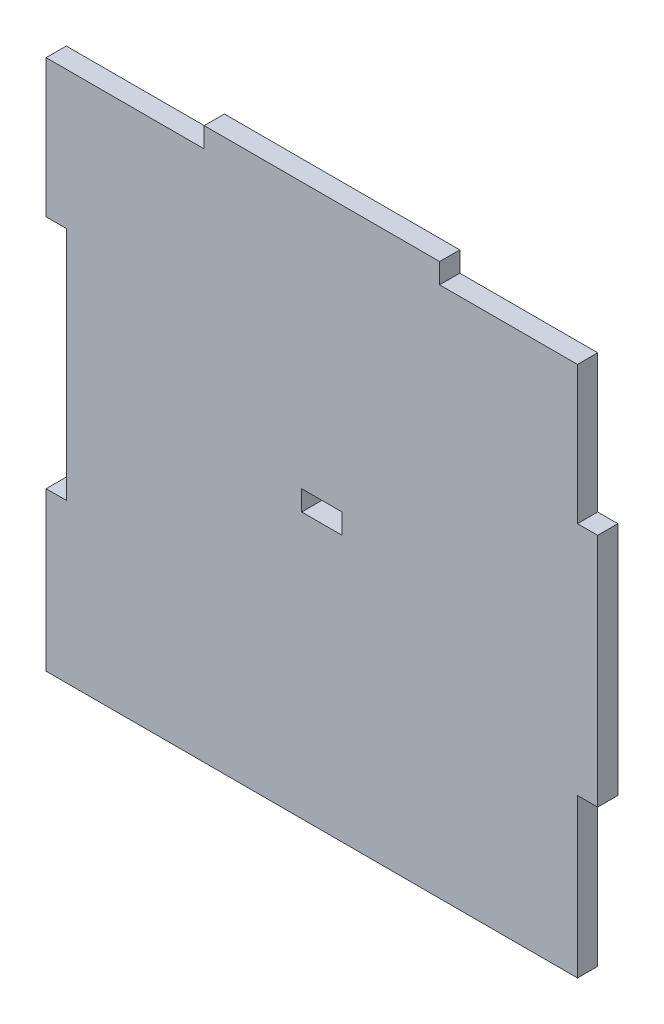
SolidWorks part; units mm, degrees
ref_plane "Front Plane" through (0, 0, 0) normal (0, 0, 1) x (1, 0, 0)
ref_plane "Top Plane" through (0, 0, 0) normal (0, 1, 0) x (1, 0, 0)
ref_plane "Right Plane" through (0, 0, 0) normal (1, 0, 0) x (0, 0, -1)
sketch "Sketch1" plane through (0, 0, 0) normal (0, 0, 1) x (1, 0, 0)
  line L0 (0, 38) -> (0, -39.5) construction
  line L5 (-38, 39.5) -> (-17.5, 39.5)
  line L6 (-38, 16) -> (-38, -16)
  line L24 (38, 39.5) -> (38, 19)
  line L26 (-41, -39.5) -> (38, -39.5)
  line L27 (-38, 0) -> (38, 0) construction
  line L28 (-17.5, 39.5) -> (-17.5, 42.5)
  line L29 (-17.5, 42.5) -> (17.5, 42.5)
  line L30 (17.5, 42.5) -> (17.5, 39.5)
  line L33 (-41, 19) -> (-41, 39.5)
  line L34 (-41, 39.5) -> (-38, 39.5)
  line L35 (-41, -19) -> (-41, -39.5)
  line L36 (38, -19) -> (38, -39.5)
  line L43 (41, 16) -> (41, -16)
  line L44 (-38, 16) -> (-38, 19)
  line L46 (17.5, 39.5) -> (38, 39.5)
  line L48 (-38, 19) -> (-41, 19)
  line L50 (-41, -19) -> (-41, -16)
  line L51 (-41, -16) -> (-38, -16)
  line L52 (38, -19) -> (38, -16)
  line L53 (38, -16) -> (41, -16)
  line L54 (41, 16) -> (41, 19)
  line L55 (41, 19) -> (38, 19)
  point P0 (0, 0)
  dimension "D1" = 79
  dimension "D2" = 76
  dimension "D3" = 3
  dimension "D4" = 35
  dimension "D5" = 3
  dimension "D6" = 76
  dimension "D7" = 35
  dimension "D8" = 3
  dimension "D9" = 3
  dimension "D10" = 3
  dimension "D11" = 3
  dimension "D12" = 35
  dimension "D13" = 0
  dimension "D14" = 20.5
extrude "Boss-Extrude1" add sketch "Sketch1" along normal blind 3
sketch "Sketch2" plane through (0, 0, 3) normal (0, 0, 1) x (1, 0, 0)
  line L0 (-41, -39.5) -> (38, -39.5) construction
  line L5 (-3, 3) -> (3, 3)
  line L6 (-3, 3) -> (-3, 0)
  line L7 (-3, 0) -> (3, 0)
  line L8 (3, 3) -> (3, 0)
  line L9 (-3, 3) -> (3, 0) construction
  line L10 (-3, 0) -> (3, 3) construction
  point P0 (0, 0)
  point P1 (0, 1.5)
  dimension "D1" = 6
  dimension "D2" = 3
  dimension "D3" = 0
  dimension "D4" = 41
extrude "Cut-Extrude1" cut sketch "Sketch2" against normal blind 3
